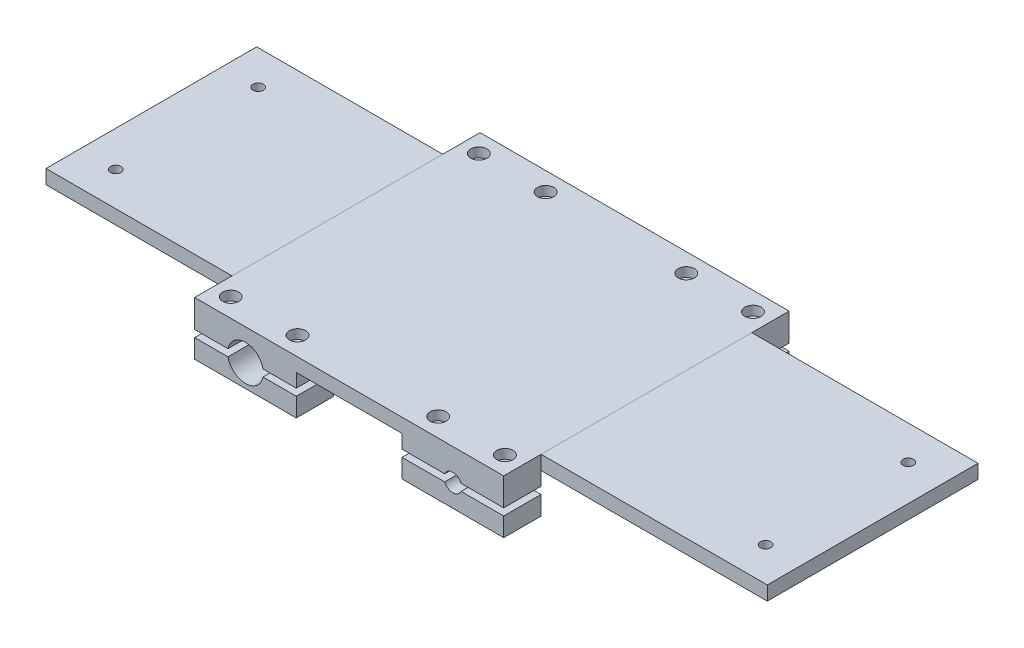
SolidWorks part; units mm, degrees
ref_plane "Front Plane" through (0, 0, 0) normal (0, 0, 1) x (1, 0, 0)
ref_plane "Top Plane" through (0, 0, 0) normal (0, 1, 0) x (1, 0, 0)
ref_plane "Right Plane" through (0, 0, 0) normal (1, 0, 0) x (0, 0, -1)
sketch "Sketch1" plane through (0, 0, 0) normal (0, 0, 1) x (1, 0, 0)
  line L0 (73.8188, 0) -> (0, 0) construction
  line L1 (-110, -15.875) -> (110, -15.875)
  line L2 (-110, -15.875) -> (-110, 15.875)
  line L3 (-110, 15.875) -> (110, 15.875)
  line L4 (110, -15.875) -> (110, 15.875)
  line L5 (-110, -15.875) -> (110, 15.875) construction
  line L6 (-110, 15.875) -> (110, -15.875) construction
  line L7 (0, 0) -> (-73.8187, 0) construction
  circle A1 centre (-73.8187, 0) radius 12.7
  circle A2 centre (73.8188, 0) radius 6.35
  point P0 (0, 0)
  dimension "D1" = 147.6375
  dimension "D4" = 25.4
  dimension "D5" = 12.7
  dimension "D2" = 31.75
  dimension "D3" = 220
extrude "Boss-Extrude1" add sketch "Sketch1" along normal blind 203.2
sketch "Sketch3" plane through (0, 0, 203.2) normal (0, 0, 1) x (1, 0, 0)
  line L0 (110, -15.875) -> (110, 15.875) construction
  line L1 (-110, 15.875) -> (110, 15.875)
  line L2 (-110, 15.875) -> (-110, 22.225)
  line L3 (-110, 22.225) -> (110, 22.225)
  line L4 (110, 15.875) -> (110, 22.225)
  dimension "D1" = 6.35
extrude "Boss-Extrude2" add sketch "Sketch3" against normal up to surface (203.2 mm away) up to face at (-61.1187, 0, 0)
sketch "Sketch4" plane through (-110, 0, 0) normal (-1, 0, 0) x (0, 0, 1)
  line L0 (203.2, -15.875) -> (0, -15.875) construction
  line L1 (26.6, -15.875) -> (176.6, -15.875)
  line L2 (26.6, -15.875) -> (26.6, 12.225)
  line L3 (26.6, 12.225) -> (176.6, 12.225)
  line L4 (176.6, -15.875) -> (176.6, 12.225)
  line L5 (0, 0) -> (26.6, 0) construction
  line L6 (26.6, 0) -> (176.6, 0) construction
  line L7 (176.6, 0) -> (203.2, 0) construction
  line L8 (203.2, 22.225) -> (203.2, -15.875) construction
  line L9 (0, 22.225) -> (203.2, 22.225) construction
  dimension "D1" = 10
  dimension "D2" = 150
extrude "Cut-Extrude1" cut sketch "Sketch4" against normal blind 253.2
sketch "Sketch5" plane through (0, 0, 0) normal (0, 0, -1) x (-1, 0, 0)
  line L0 (110, -15.875) -> (-110, -15.875) construction
  line L1 (-37.6375, -15.875) -> (37.6375, -15.875)
  line L2 (-37.6375, -15.875) -> (-37.6375, 12.225)
  line L3 (-37.6375, 12.225) -> (37.6375, 12.225)
  line L4 (37.6375, -15.875) -> (37.6375, 12.225)
  line L5 (-110, 22.225) -> (110, 22.225) construction
  line L6 (0, 0) -> (-37.6375, 0) construction
  line L7 (0, 0) -> (37.6375, 0) construction
  line L8 (-37.6375, 0) -> (-73.8188, 0) construction
  line L9 (-73.8188, 0) -> (-110, 0) construction
  line L10 (-110, -15.875) -> (-110, 22.225) construction
  dimension "D1" = 10
extrude "Cut-Extrude2" cut sketch "Sketch5" against normal blind 203.2
sketch "Sketch6" plane through (0, -15.875, 0) normal (0, -1, 0) x (1, 0, 0)
  line L0 (-110, 189.9) -> (-97.5688, 189.9) construction
  line L2 (-97.5688, 189.9) -> (-50.0688, 189.9) construction
  line L3 (-50.0688, 189.9) -> (-37.6375, 189.9) construction
  line L5 (-110, 13.3) -> (-97.5688, 13.3) construction
  line L6 (-110, 26.6) -> (-110, 0) construction
  line L7 (-97.5688, 13.3) -> (-50.0688, 13.3) construction
  line L8 (-50.0688, 13.3) -> (-37.6375, 13.3) construction
  line L9 (-37.6375, 26.6) -> (-37.6375, 0) construction
  line L10 (37.6375, 203.2) -> (37.6375, 176.6) construction
  line L11 (37.6375, 26.6) -> (37.6375, 0) construction
  line L12 (37.6375, 13.3) -> (50.0688, 13.3) construction
  line L13 (50.0688, 13.3) -> (97.5687, 13.3) construction
  line L14 (97.5687, 13.3) -> (110, 13.3) construction
  line L16 (-61.1187, 203.2) -> (-86.5187, 203.2) construction
  line L18 (110, 189.9) -> (97.5687, 189.9) construction
  line L19 (97.5687, 189.9) -> (50.0688, 189.9) construction
  line L20 (50.0688, 189.9) -> (37.6375, 189.9) construction
  line L22 (-61.1187, 203.2) -> (-86.5187, 203.2)
  line L23 (-86.5187, 203.2) -> (-86.5187, 0) construction
  line L24 (-110, 0) -> (-37.6375, 0) construction
  line L25 (-61.1187, 203.2) -> (-61.1187, 0) construction
  line L28 (-37.6375, 203.2) -> (-37.6375, 176.6) construction
  line L29 (-110, 203.2) -> (-110, 176.6) construction
  line L30 (110, 203.2) -> (110, 176.6) construction
  circle A0 centre (-50.0688, 189.9) radius 3.7258
  circle A1 centre (-97.5688, 189.9) radius 3.7258
  circle A2 centre (-97.5688, 13.3) radius 3.7258
  circle A3 centre (-50.0688, 13.3) radius 3.7258
  circle A4 centre (50.0688, 13.3) radius 3.7258
  circle A5 centre (97.5687, 13.3) radius 3.7258
  circle A6 centre (97.5687, 189.9) radius 3.7258
  circle A7 centre (50.0688, 189.9) radius 3.7258
  dimension "D1" = 7.4516
  dimension "D2" = 47.5
extrude "Cut-Extrude3" cut sketch "Sketch6" against normal blind 203.2 contours A4 | A5 | A3 | A2 | A1 | A0 | A7 | A6
sketch "Sketch7" plane through (0, 0, 0) normal (0, 0, -1) x (-1, 0, 0)
  line L0 (-110, -15.875) -> (-110, 22.225) construction
  line L1 (110, -2.5) -> (-110, -2.5)
  line L2 (110, -2.5) -> (110, 2.5)
  line L3 (110, 2.5) -> (-110, 2.5)
  line L4 (-110, -2.5) -> (-110, 2.5)
  line L5 (110, -2.5) -> (-110, 2.5) construction
  line L6 (110, 2.5) -> (-110, -2.5) construction
  point P0 (0, 0)
  dimension "D1" = 5
extrude "Cut-Extrude4" cut sketch "Sketch7" against normal blind 203.2
sketch "Sketch8" plane through (-110, 0, 0) normal (-1, 0, 0) x (0, 0, 1)
  line L0 (176.6, 12.225) -> (26.6, 12.225) construction
  line L1 (176.6, 12.225) -> (26.6, 12.225)
  line L2 (176.6, 12.225) -> (176.6, 22.225)
  line L3 (176.6, 22.225) -> (26.6, 22.225)
  line L4 (26.6, 12.225) -> (26.6, 22.225)
  line L5 (0, 22.225) -> (203.2, 22.225) construction
  line M4 (26.6, 12.225) -> (176.6, 12.225)
  line M8 (203.2, 22.225) -> (0, 22.225)
extrude "Boss-Extrude3" add sketch "Sketch8" along normal blind 132.4137 contours L4 L2 M4 M8
sketch "Sketch9" plane through (110, 0, 0) normal (1, 0, 0) x (0, 0, -1)
  line L0 (-176.6, 12.225) -> (-26.6, 12.225) construction
  line L1 (-176.6, 12.225) -> (-26.6, 12.225)
  line L2 (-176.6, 12.225) -> (-176.6, 22.225)
  line L3 (-176.6, 22.225) -> (-26.6, 22.225)
  line L4 (-26.6, 12.225) -> (-26.6, 22.225)
  line L5 (0, 22.225) -> (-203.2, 22.225) construction
extrude "Boss-Extrude4" add sketch "Sketch9" along normal blind 161.0473
ref_plane "Plane1" through (-110, 0, 0) normal (-1, 0, 0) x (0, 0, 1)
ref_plane "Plane2" through (110, 0, 0) normal (1, 0, 0) x (0, 0, -1)
split line "Split Line1"
split line "Split Line2"
sketch "Sketch10" plane through (0, 22.225, 0) normal (0, 1, 0) x (1, 0, 0)
  line L1 (0, 0) -> (0, -203.2) construction
  line L3 (110, 0) -> (-110, 0) construction
  line L4 (110, -203.2) -> (-110, -203.2) construction
  line L5 (-217.0137, -152.4) -> (245.6473, -152.4) construction
  circle A8 centre (-217.0137, -152.4) radius 3.7258
  circle A9 centre (-217.0137, -50.9667) radius 3.7258
  circle A10 centre (245.6473, -50.8) radius 3.7258
  circle A11 centre (245.6473, -152.4) radius 3.7258
  dimension "D1" = 7.4516
extrude "Cut-Extrude5" cut sketch "Sketch10" against normal blind 10
sketch "Sketch11" plane through (0, 22.225, 0) normal (0, 1, 0) x (1, 0, 0)
  circle A0 centre (97.5687, -13.3) radius 5.7625
  circle A1 centre (50.0688, -13.3) radius 5.7625
  circle A2 centre (97.5687, -189.9) radius 5.7625
  circle A3 centre (50.0688, -189.9) radius 5.7625
  circle A4 centre (-50.0688, -189.9) radius 5.7625
  circle A5 centre (-97.5688, -189.9) radius 5.7625
  circle A6 centre (-97.5688, -13.3) radius 5.7625
  circle A7 centre (-50.0688, -13.3) radius 5.7625
  dimension "D1" = 11.525
extrude "Cut-Extrude6" cut sketch "Sketch11" against normal blind 6.6675
